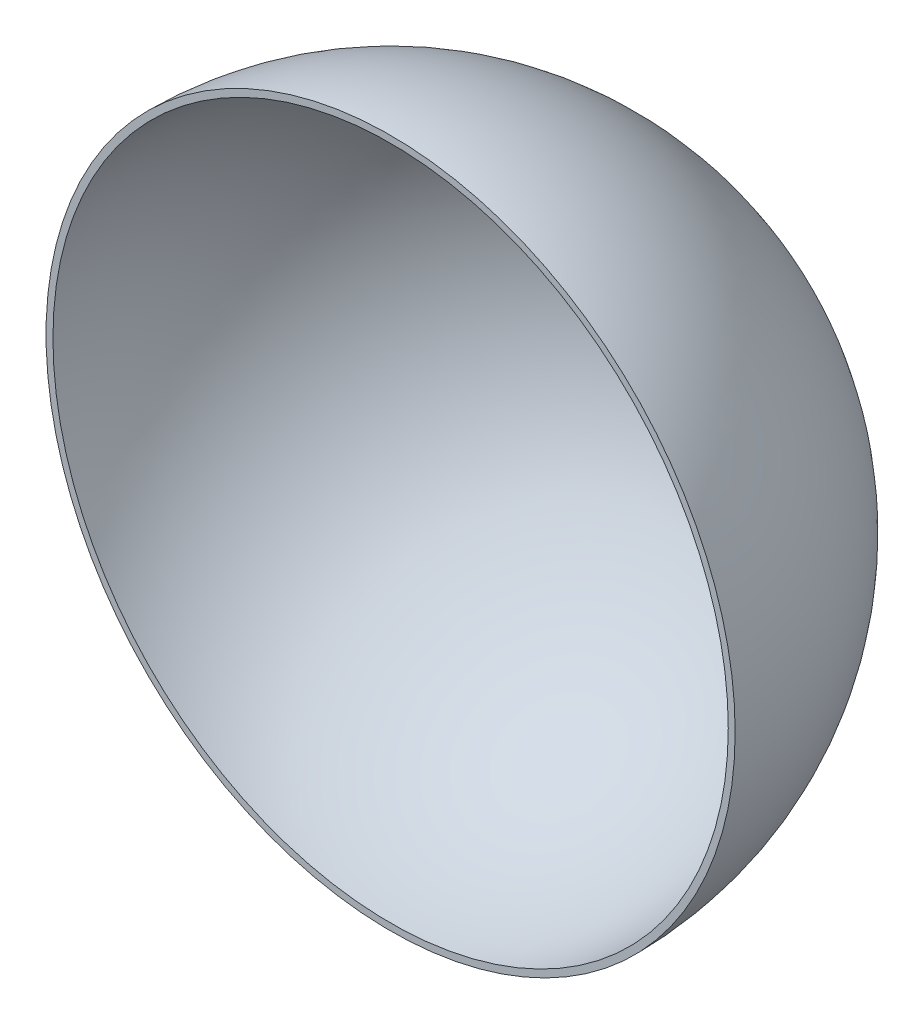
SolidWorks part; units mm, degrees
ref_plane "前视基准面" through (0, 0, 0) normal (0, 0, 1) x (1, 0, 0)
ref_plane "上视基准面" through (0, 0, 0) normal (0, 1, 0) x (1, 0, 0)
ref_plane "右视基准面" through (0, 0, 0) normal (1, 0, 0) x (0, 0, -1)
sketch "草图1" plane through (0, 0, 0) normal (0, 0, 1) x (1, 0, 0)
  line L0 (0, 100) -> (0, -100)
  arc A0 (0, -100) -> (0, 100) centre (0, 0) ccw
  dimension "D1" = 200
revolve "旋转7" add sketch "草图1" angle 360 about L0
sketch "草图3" plane through (0, 0, 0) normal (0, 0, 1) x (1, 0, 0)
  line L0 (0, 98) -> (0, -98)
  arc A0 (0, -98) -> (0, 98) centre (0, 0) ccw
  dimension "D1" = 98
revolve "切除-旋转1" cut sketch "草图3" angle 360 about L0
sketch "草图2" plane through (0, 0, 0) normal (0, 0, 1) x (1, 0, 0)
  circle A0 centre (0, 0) radius 100
  dimension "D1" = 200
extrude "切除-拉伸1" cut sketch "草图2" along normal through all
